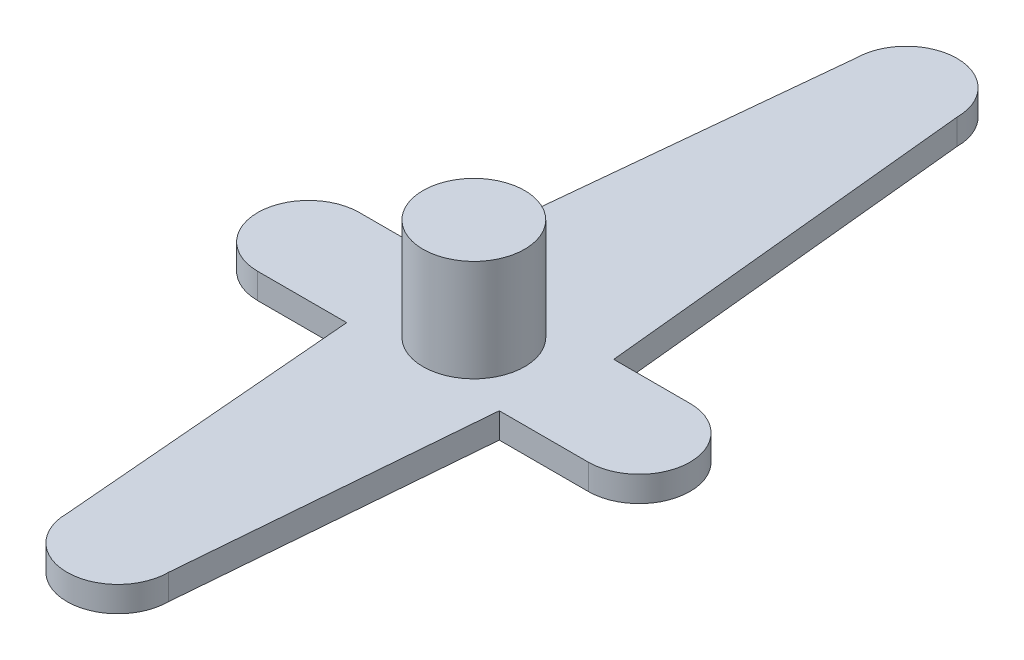
SolidWorks part; units mm, degrees
material "ABS"
ref_plane "Front Plane" through (0, 0, 0) normal (0, 0, 1) x (1, 0, 0)
ref_plane "Top Plane" through (0, 0, 0) normal (0, 1, 0) x (1, 0, 0)
ref_plane "Right Plane" through (0, 0, 0) normal (1, 0, 0) x (0, 0, -1)
sketch "Sketch1" plane through (0, 0, 0) normal (0, 1, 0) x (1, 0, 0)
  line L0 (-6.5, 0) -> (6.5, 0) construction
  line L1 (-6.5, 2) -> (6.5, 2)
  line L2 (-6.5, -2) -> (6.5, -2)
  line L3 (-3.5, 2) -> (-2, 17)
  line L4 (3.5, 2) -> (2, 17)
  line L5 (-3, -2) -> (-2, -14)
  line L6 (3, -2) -> (2, -14)
  arc A0 (-6.5, 2) -> (-6.5, -2) centre (-6.5, 0) ccw
  arc A1 (6.5, -2) -> (6.5, 2) centre (6.5, 0) ccw
  arc A2 (-2, 17) -> (2, 17) centre (0, 17) cw
  arc A3 (-2, -14) -> (2, -14) centre (0, -14) ccw
  point P3 (0, 0)
  point P14 (0, 2)
  point P18 (0, -2)
  point P20 (0, 0)
  point P21 (0, 0)
  point P22 (3, -2)
  point P23 (-1.2444, -14)
  point P24 (0, 0)
  dimension "D2" = 2
  dimension "D5" = 2
  dimension "D9" = 2
  dimension "D1" = 13
  dimension "D3" = 7
  dimension "D4" = 3.5
  dimension "D6" = 15
  dimension "D7" = 6
  dimension "D8" = 3
  dimension "D10" = 12
extrude "Boss-Extrude1" add sketch "Sketch1" along normal blind 1
sketch "Sketch2" plane through (0, 1, 0) normal (0, 1, 0) x (1, 0, 0)
  circle A0 centre (0, 0) radius 2
  dimension "D1" = 4
extrude "Boss-Extrude2" add sketch "Sketch2" along normal blind 4
